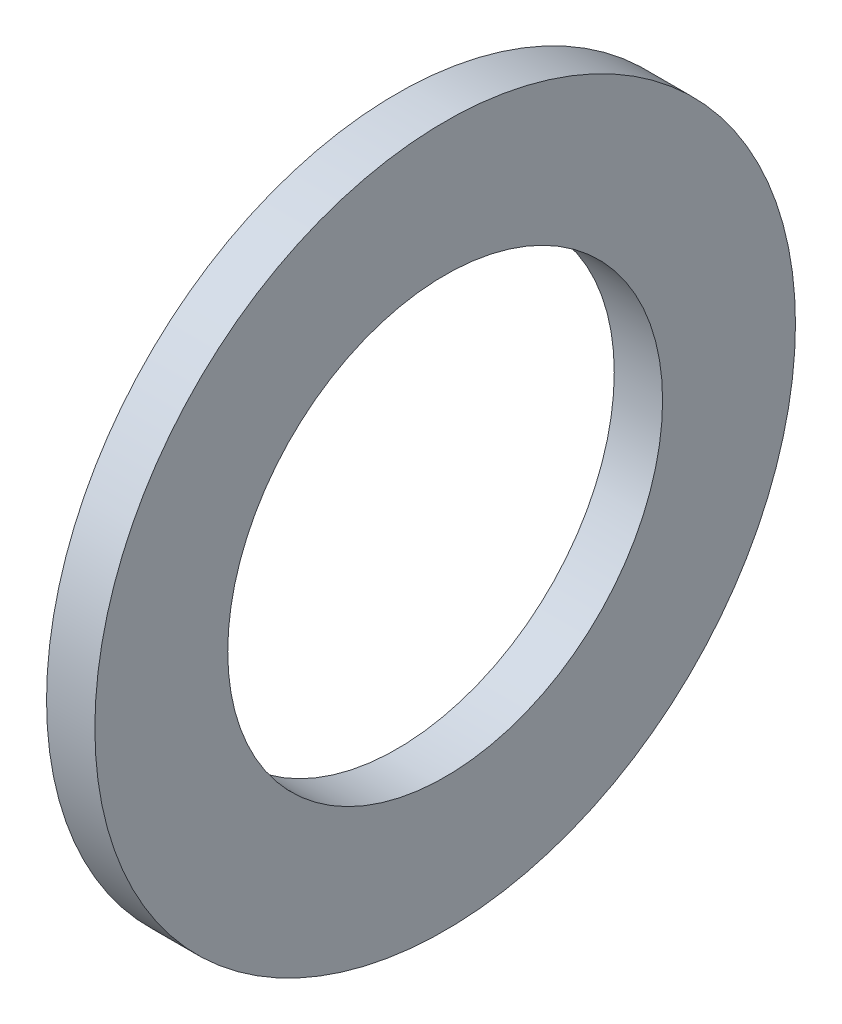
SolidWorks part; units mm, degrees
ref_plane "Front Plane" through (0, 0, 0) normal (0, 0, 1) x (1, 0, 0)
ref_plane "Top Plane" through (0, 0, 0) normal (0, 1, 0) x (1, 0, 0)
ref_plane "Right Plane" through (0, 0, 0) normal (1, 0, 0) x (0, 0, -1)
sketch "Sketch1" plane through (0, 0, 0) normal (0, 1, 0) x (1, 0, 0)
  line L0 (-89.8649, 0) -> (0, 0) construction
  line L1 (0, 0) -> (0, -6.7901) construction
  line L2 (0, -18) -> (-4, -18)
  line L3 (0, -18) -> (0, -29)
  line L4 (0, -29) -> (-4, -29)
  line L5 (-4, -18) -> (-4, -29)
  line L6 (0, -18) -> (-4, -29) construction
  line L7 (0, -29) -> (-4, -18) construction
  point P1 (-2, -23.5)
  dimension "D1" = 18
  dimension "D2" = 29
  dimension "D3" = 4
revolve "Revolve1" add sketch "Sketch1" angle 360 about L0
